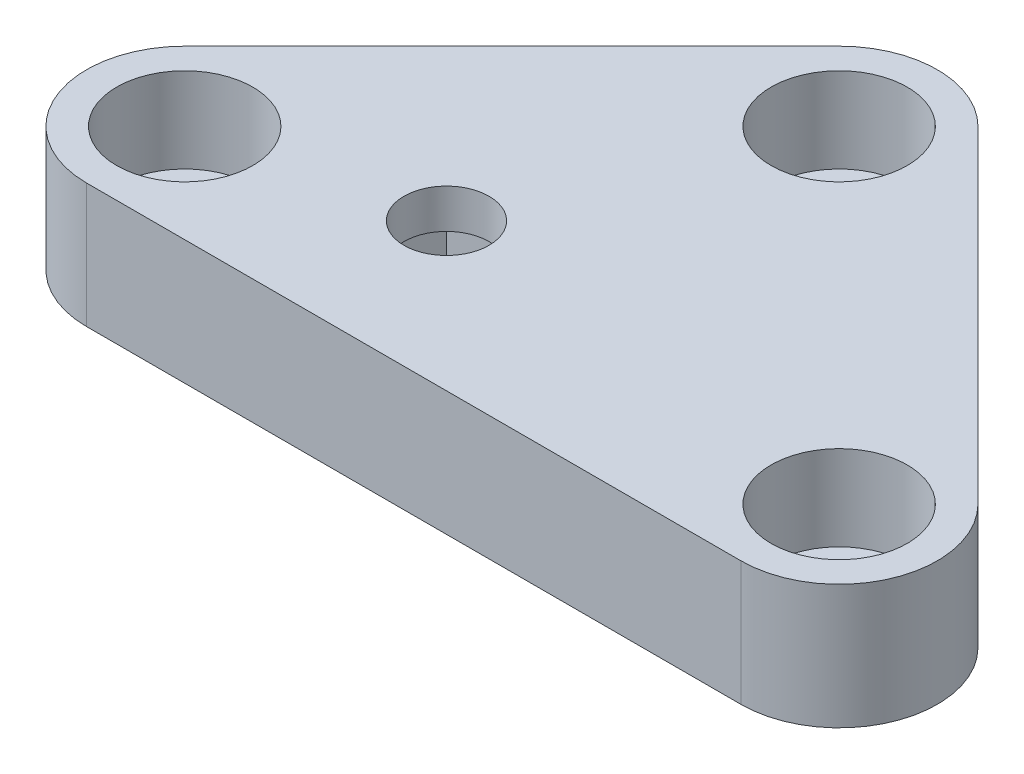
SolidWorks part; units mm, degrees
ref_plane "정면" through (0, 0, 0) normal (0, 0, 1) x (1, 0, 0)
ref_plane "윗면" through (0, 0, 0) normal (0, 1, 0) x (1, 0, 0)
ref_plane "우측면" through (0, 0, 0) normal (1, 0, 0) x (0, 0, -1)
sketch "스케치1" plane through (0, 0, 0) normal (0, 1, 0) x (1, 0, 0)
  line L0 (0, 0) -> (80, -80) construction
  line L1 (0, 0) -> (-80, -80) construction
  line L2 (0, 0) -> (0, -80) construction
  line L3 (3.4467, -53.4467) -> (-21.5533, -78.4467)
  line L4 (-16.25, -91.25) -> (33.75, -91.25)
  line L5 (14.0533, -53.4467) -> (39.0533, -78.4467)
  circle A0 centre (0, -80) radius 3.25
  circle A1 centre (-16.25, -83.75) radius 3.2
  circle A2 centre (8.75, -58.75) radius 3.2
  arc A3 (14.0533, -53.4467) -> (3.4467, -53.4467) centre (8.75, -58.75) ccw
  circle A4 centre (33.75, -83.75) radius 3.2
  arc A5 (33.75, -91.25) -> (39.0533, -78.4467) centre (33.75, -83.75) ccw
  arc A6 (-21.5533, -78.4467) -> (-16.25, -91.25) centre (-16.25, -83.75) ccw
  point P2 (0, 0)
  point P4 (33.75, -33.75)
  point P5 (33.75, -33.75)
  point P6 (33.75, -58.75)
  point P7 (33.75, -83.75)
  point P8 (8.75, -58.75)
  point P9 (8.75, -83.75)
  point P10 (-16.25, -58.75)
  point P11 (-16.25, -83.75)
  point P22 (-33.75, -33.75)
  dimension "D2" = 6.5
  dimension "D9" = 6.4
  dimension "D13" = 15
  dimension "D1" = 80
  dimension "D3" = 33.75
  dimension "D4" = 33.75
  dimension "D5" = 25
  dimension "D6" = 25
  dimension "D7" = 25
  dimension "D8" = 50
  dimension "D10" = 45
  dimension "D11" = 45
  dimension "D12" = 33.75
extrude "보스-돌출1" add sketch "스케치1" along normal blind 9.5
sketch "스케치2" plane through (0, 9.5, 0) normal (0, 1, 0) x (1, 0, 0)
  circle A0 centre (8.75, -58.75) radius 5.2
  circle A1 centre (33.75, -83.75) radius 5.2
  circle A2 centre (-16.25, -83.75) radius 5.2
  circle A3 centre (-16.25, -83.75) radius 3.2 construction
  circle A4 centre (8.75, -58.75) radius 3.2 construction
  circle A5 centre (33.75, -83.75) radius 3.2 construction
  dimension "D1" = 10.4
extrude "컷-돌출1" cut sketch "스케치2" against normal blind 6.5
sketch "스케치3" plane through (0, 0, 0) normal (0, -1, 0) x (1, 0, 0)
  line L1 (-5.2, 85.2) -> (5.2, 85.2)
  line L2 (-5.2, 85.2) -> (-5.2, 74.8)
  line L3 (-5.2, 74.8) -> (5.2, 74.8)
  line L4 (5.2, 85.2) -> (5.2, 74.8)
  circle A0 centre (0, 80) radius 3.25
  circle A1 centre (0, 80) radius 3.25 construction
  point P7 (0, 80)
  point P8 (0, 0)
  point P9 (5.2, 80)
  point P10 (0, 85.2)
  point P11 (0, 80)
  dimension "D1" = 10.4
  dimension "D2" = 10.4
extrude "컷-돌출2" cut sketch "스케치3" against normal blind 6.5
